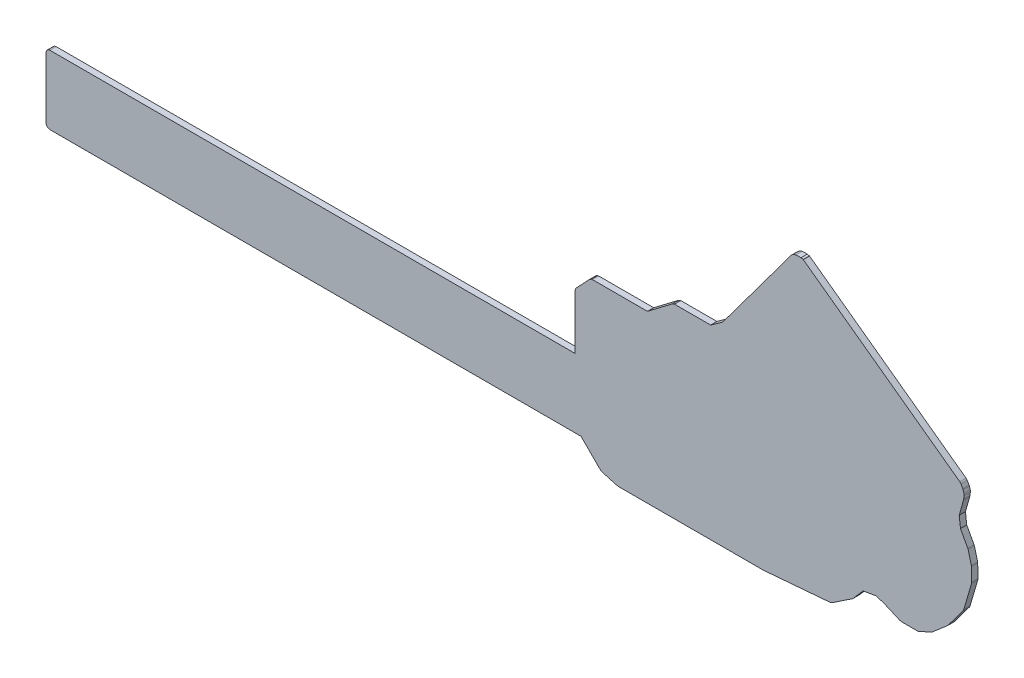
SolidWorks part; units mm, degrees
ref_plane "Front Plane" through (0, 0, 0) normal (0, 0, 1) x (1, 0, 0)
ref_plane "Top Plane" through (0, 0, 0) normal (0, 1, 0) x (1, 0, 0)
ref_plane "Right Plane" through (0, 0, 0) normal (1, 0, 0) x (0, 0, -1)
sketch "Model" plane through (0, 0, 0) normal (0, 0, 1) x (1, 0, 0)
  line L0 (-0.719, 4.4763) -> (-0.709, 4.4703)
  line L1 (-0.709, 4.4703) -> (4.285, 0.8313)
  line L2 (4.285, 0.8313) -> (4.319, 0.7923)
  line L3 (4.319, 0.7923) -> (4.38, 0.6863)
  line L4 (4.38, 0.6863) -> (4.39, 0.6633)
  line L5 (4.39, 0.6633) -> (4.417, 0.5823)
  line L6 (4.417, 0.5823) -> (4.423, 0.5273)
  line L7 (4.423, 0.5273) -> (4.407, 0.4043)
  line L8 (4.407, 0.4043) -> (4.404, 0.3863)
  line L9 (4.404, 0.3863) -> (4.266, -0.1047)
  line L10 (4.266, -0.1047) -> (4.306, -0.4547)
  line L11 (4.306, -0.4547) -> (4.539, -0.8817)
  line L12 (4.539, -0.8817) -> (4.55, -0.9097)
  line L13 (4.55, -0.9097) -> (4.652, -1.3007)
  line L14 (4.652, -1.3007) -> (4.656, -1.3297)
  line L15 (4.656, -1.3297) -> (4.666, -1.7557)
  line L16 (4.666, -1.7557) -> (4.661, -1.7927)
  line L17 (4.661, -1.7927) -> (4.412, -2.6427)
  line L18 (4.412, -2.6427) -> (4.393, -2.6827)
  line L19 (4.393, -2.6827) -> (3.914, -3.3237)
  line L20 (3.914, -3.3237) -> (3.896, -3.3437)
  line L21 (3.896, -3.3437) -> (3.419, -3.7537)
  line L22 (3.419, -3.7537) -> (3.391, -3.7717)
  line L23 (3.391, -3.7717) -> (2.991, -3.9627)
  line L24 (2.991, -3.9627) -> (2.938, -3.9747)
  line L25 (2.938, -3.9747) -> (2.422, -3.9747)
  line L26 (2.422, -3.9747) -> (2.372, -3.9647)
  line L27 (2.372, -3.9647) -> (1.866, -3.7447)
  line L28 (1.866, -3.7447) -> (1.606, -3.6647)
  line L29 (1.606, -3.6647) -> (1.196, -3.7347)
  line L30 (1.196, -3.7347) -> (0.877, -4.1017)
  line L31 (0.877, -4.1017) -> (0.852, -4.1237)
  line L32 (0.852, -4.1237) -> (0.203, -4.5567)
  line L33 (0.203, -4.5567) -> (0.144, -4.5777)
  line L34 (0.144, -4.5777) -> (-1.991, -4.7547)
  line L35 (-1.991, -4.7547) -> (-1.997, -4.7547)
  line L36 (-1.997, -4.7547) -> (-6.627, -4.7547)
  line L37 (-6.627, -4.7547) -> (-6.66, -4.7497)
  line L38 (-6.66, -4.7497) -> (-7.143, -4.6137)
  line L39 (-7.143, -4.6137) -> (-7.197, -4.5817)
  line L40 (-7.197, -4.5817) -> (-7.814, -3.9647)
  line L41 (-7.814, -3.9647) -> (-7.999, -3.9647)
  line L42 (-7.999, -3.9647) -> (-8.005, -3.9627)
  line L43 (-8.005, -3.9627) -> (-24.783, -3.9627)
  line L44 (-24.783, -3.9627) -> (-24.85, -3.9427)
  line L45 (-24.85, -3.9427) -> (-24.896, -3.8907)
  line L46 (-24.896, -3.8907) -> (-24.907, -3.8387)
  line L47 (-24.907, -3.8387) -> (-24.907, -1.8897)
  line L48 (-24.907, -1.8897) -> (-24.888, -1.8227)
  line L49 (-24.888, -1.8227) -> (-24.835, -1.7767)
  line L50 (-24.835, -1.7767) -> (-24.783, -1.7657)
  line L51 (-24.783, -1.7657) -> (-8.005, -1.7657)
  line L52 (-8.005, -1.7657) -> (-8.004, -1.7647)
  line L53 (-8.004, -1.7647) -> (-8.004, -0.0237)
  line L54 (-8.004, -0.0237) -> (-7.984, 0.0433)
  line L55 (-7.984, 0.0433) -> (-7.97, 0.0613)
  line L56 (-7.97, 0.0613) -> (-7.541, 0.5163)
  line L57 (-7.541, 0.5163) -> (-7.48, 0.5513)
  line L58 (-7.48, 0.5513) -> (-7.45, 0.5553)
  line L59 (-7.45, 0.5553) -> (-5.694, 0.5553)
  line L60 (-5.694, 0.5553) -> (-4.897, 1.1603)
  line L61 (-4.897, 1.1603) -> (-4.832, 1.1853)
  line L62 (-4.832, 1.1853) -> (-4.822, 1.1853)
  line L63 (-4.822, 1.1853) -> (-3.674, 1.1853)
  line L64 (-3.674, 1.1853) -> (-3.284, 1.4653)
  line L65 (-3.284, 1.4653) -> (-1.099, 4.4053)
  line L66 (-1.099, 4.4053) -> (-1.063, 4.4383)
  line L67 (-1.063, 4.4383) -> (-1.011, 4.4693)
  line L68 (-1.011, 4.4693) -> (-0.952, 4.4863)
  line L69 (-0.952, 4.4863) -> (-0.787, 4.4933)
  line L70 (-0.787, 4.4933) -> (-0.719, 4.4763)
  line L71 (-12.208, 15.5833) -> (-12.129, 15.5673)
  line L72 (-12.129, 15.5673) -> (-12.085, 15.5493)
  line L73 (-12.085, 15.5493) -> (-12.028, 15.5113)
  line L74 (-12.028, 15.5113) -> (-11.994, 15.4773)
  line L75 (-11.994, 15.4773) -> (-11.957, 15.4203)
  line L76 (-11.957, 15.4203) -> (-11.938, 15.3763)
  line L77 (-11.938, 15.3763) -> (-11.922, 15.2973)
  line L78 (-11.922, 15.2973) -> (-11.92, 15.2733)
  line L79 (-11.92, 15.2733) -> (-11.92, 14.0013)
  line L80 (-11.92, 14.0013) -> (-11.922, 13.9773)
  line L81 (-11.922, 13.9773) -> (-11.938, 13.8983)
  line L82 (-11.938, 13.8983) -> (-11.957, 13.8543)
  line L83 (-11.957, 13.8543) -> (-11.994, 13.7973)
  line L84 (-11.994, 13.7973) -> (-12.028, 13.7633)
  line L85 (-12.028, 13.7633) -> (-12.085, 13.7253)
  line L86 (-12.085, 13.7253) -> (-12.129, 13.7073)
  line L87 (-12.129, 13.7073) -> (-12.208, 13.6913)
  line L88 (-12.208, 13.6913) -> (-12.232, 13.6893)
  line L89 (-12.232, 13.6893) -> (-12.403, 13.6893)
  line L90 (-12.403, 13.6893) -> (-12.518, 13.6663)
  line L91 (-12.518, 13.6663) -> (-12.615, 13.6013)
  line L92 (-12.615, 13.6013) -> (-12.68, 13.5043)
  line L93 (-12.68, 13.5043) -> (-12.703, 13.3893)
  line L94 (-12.703, 13.3893) -> (-12.703, 10.1123)
  line L95 (-12.703, 10.1123) -> (-12.705, 10.0883)
  line L96 (-12.705, 10.0883) -> (-12.721, 10.0093)
  line L97 (-12.721, 10.0093) -> (-12.739, 9.9643)
  line L98 (-12.739, 9.9643) -> (-12.777, 9.9083)
  line L99 (-12.777, 9.9083) -> (-12.811, 9.8743)
  line L100 (-12.811, 9.8743) -> (-12.868, 9.8363)
  line L101 (-12.868, 9.8363) -> (-12.912, 9.8183)
  line L102 (-12.912, 9.8183) -> (-12.991, 9.8023)
  line L103 (-12.991, 9.8023) -> (-13.015, 9.8003)
  line L104 (-13.015, 9.8003) -> (-14.285, 9.8003)
  line L105 (-14.285, 9.8003) -> (-14.361, 9.7843)
  line L106 (-14.361, 9.7843) -> (-14.426, 9.7413)
  line L107 (-14.426, 9.7413) -> (-14.47, 9.6763)
  line L108 (-14.47, 9.6763) -> (-14.485, 9.6003)
  line L109 (-14.485, 9.6003) -> (-14.485, 9.0813)
  line L110 (-14.485, 9.0813) -> (-14.487, 9.0573)
  line L111 (-14.487, 9.0573) -> (-14.495, 9.0173)
  line L112 (-14.495, 9.0173) -> (-14.514, 8.9723)
  line L113 (-14.514, 8.9723) -> (-14.53, 8.9483)
  line L114 (-14.53, 8.9483) -> (-14.564, 8.9143)
  line L115 (-14.564, 8.9143) -> (-14.566, 8.9133)
  line L116 (-14.566, 8.9133) -> (-14.632, 8.8923)
  line L117 (-14.632, 8.8923) -> (-14.635, 8.8923)
  line L118 (-14.635, 8.8923) -> (-18.652, 8.8953)
  line L119 (-18.652, 8.8953) -> (-18.72, 8.9143)
  line L120 (-18.72, 8.9143) -> (-18.755, 8.9503)
  line L121 (-18.755, 8.9503) -> (-18.77, 8.9723)
  line L122 (-18.77, 8.9723) -> (-18.789, 9.0173)
  line L123 (-18.789, 9.0173) -> (-18.797, 9.0573)
  line L124 (-18.797, 9.0573) -> (-18.799, 9.0813)
  line L125 (-18.799, 9.0813) -> (-18.799, 9.6003)
  line L126 (-18.799, 9.6003) -> (-18.815, 9.6763)
  line L127 (-18.815, 9.6763) -> (-18.858, 9.7413)
  line L128 (-18.858, 9.7413) -> (-18.923, 9.7843)
  line L129 (-18.923, 9.7843) -> (-18.999, 9.8003)
  line L130 (-18.999, 9.8003) -> (-19.007, 9.8003)
  line L131 (-19.007, 9.8003) -> (-19.021, 9.8043)
  line L132 (-19.021, 9.8043) -> (-21.43, 9.8043)
  line L133 (-21.43, 9.8043) -> (-21.497, 9.8233)
  line L134 (-21.497, 9.8233) -> (-21.543, 9.8763)
  line L135 (-21.543, 9.8763) -> (-21.554, 9.9283)
  line L136 (-21.554, 9.9283) -> (-21.554, 9.9853)
  line L137 (-21.554, 9.9853) -> (-21.577, 10.1003)
  line L138 (-21.577, 10.1003) -> (-21.642, 10.1973)
  line L139 (-21.642, 10.1973) -> (-21.739, 10.2623)
  line L140 (-21.739, 10.2623) -> (-21.854, 10.2853)
  line L141 (-21.854, 10.2853) -> (-22.082, 10.2853)
  line L142 (-22.082, 10.2853) -> (-22.106, 10.2873)
  line L143 (-22.106, 10.2873) -> (-22.146, 10.2963)
  line L144 (-22.146, 10.2963) -> (-22.191, 10.3143)
  line L145 (-22.191, 10.3143) -> (-22.215, 10.3303)
  line L146 (-22.215, 10.3303) -> (-22.249, 10.3643)
  line L147 (-22.249, 10.3643) -> (-22.265, 10.3883)
  line L148 (-22.265, 10.3883) -> (-22.284, 10.4333)
  line L149 (-22.284, 10.4333) -> (-22.292, 10.4733)
  line L150 (-22.292, 10.4733) -> (-22.294, 10.4973)
  line L151 (-22.294, 10.4973) -> (-22.294, 12.4733)
  line L152 (-22.294, 12.4733) -> (-22.292, 12.4973)
  line L153 (-22.292, 12.4973) -> (-22.284, 12.5373)
  line L154 (-22.284, 12.5373) -> (-22.265, 12.5823)
  line L155 (-22.265, 12.5823) -> (-22.249, 12.6063)
  line L156 (-22.249, 12.6063) -> (-22.215, 12.6403)
  line L157 (-22.215, 12.6403) -> (-22.191, 12.6563)
  line L158 (-22.191, 12.6563) -> (-22.146, 12.6753)
  line L159 (-22.146, 12.6753) -> (-22.106, 12.6833)
  line L160 (-22.106, 12.6833) -> (-22.082, 12.6853)
  line L161 (-22.082, 12.6853) -> (-21.854, 12.6853)
  line L162 (-21.854, 12.6853) -> (-21.739, 12.7083)
  line L163 (-21.739, 12.7083) -> (-21.642, 12.7733)
  line L164 (-21.642, 12.7733) -> (-21.577, 12.8703)
  line L165 (-21.577, 12.8703) -> (-21.554, 12.9853)
  line L166 (-21.554, 12.9853) -> (-21.554, 15.2733)
  line L167 (-21.554, 15.2733) -> (-21.552, 15.2973)
  line L168 (-21.552, 15.2973) -> (-21.536, 15.3763)
  line L169 (-21.536, 15.3763) -> (-21.517, 15.4203)
  line L170 (-21.517, 15.4203) -> (-21.48, 15.4773)
  line L171 (-21.48, 15.4773) -> (-21.446, 15.5113)
  line L172 (-21.446, 15.5113) -> (-21.389, 15.5493)
  line L173 (-21.389, 15.5493) -> (-21.345, 15.5673)
  line L174 (-21.345, 15.5673) -> (-21.266, 15.5833)
  line L175 (-21.266, 15.5833) -> (-21.242, 15.5853)
  line L176 (-21.242, 15.5853) -> (-12.232, 15.5853)
  line L177 (-12.232, 15.5853) -> (-12.208, 15.5833)
extrude "Boss-Extrude1" add sketch "Model" along normal blind 0.2
delete or keep bodies "Body-Delete/Keep 1" type delete bodies bodies 102
